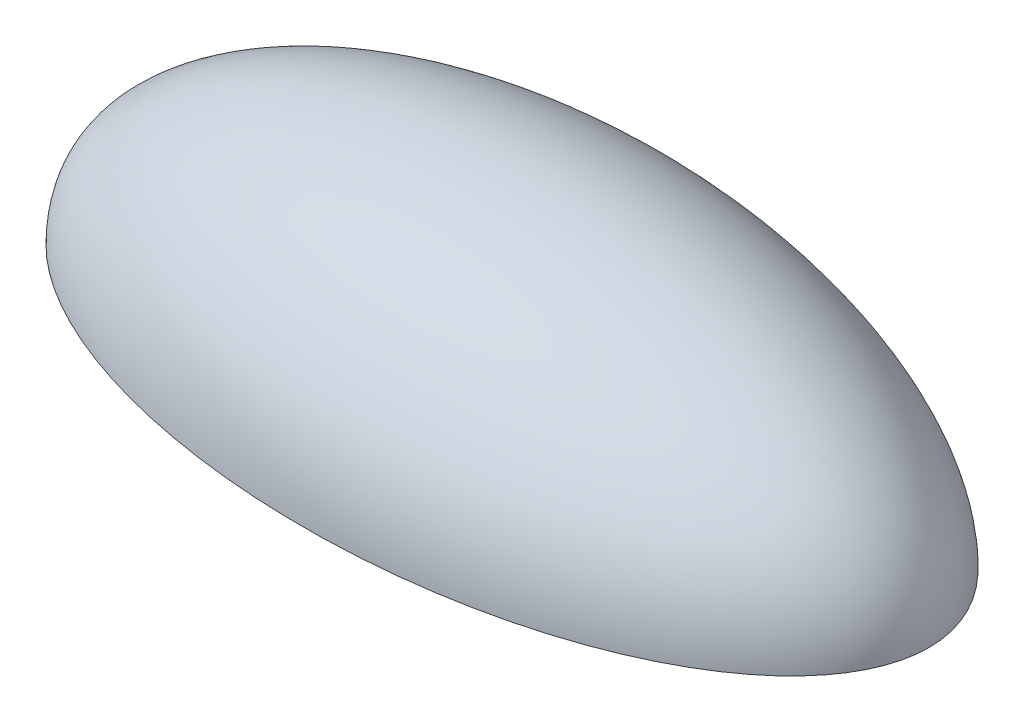
SolidWorks part; units mm, degrees
ref_plane "Front Plane" through (0, 0, 0) normal (0, 0, 1) x (1, 0, 0)
ref_plane "Top Plane" through (0, 0, 0) normal (0, 1, 0) x (1, 0, 0)
ref_plane "Right Plane" through (0, 0, 0) normal (1, 0, 0) x (0, 0, -1)
sketch "Sketch1" plane through (0, 0, 0) normal (0, 1, 0) x (1, 0, 0)
  line L0 (-12, 0) -> (12, 0)
  line L1 (0, 0) -> (0, 6) construction
  ellipse E0 centre (0, 0) end of major axis (-12, 0) minor radius 6 (12, 0) -> (-12, 0) ccw
revolve "Revolve3" add sketch "Sketch1" angle 180 about L0
